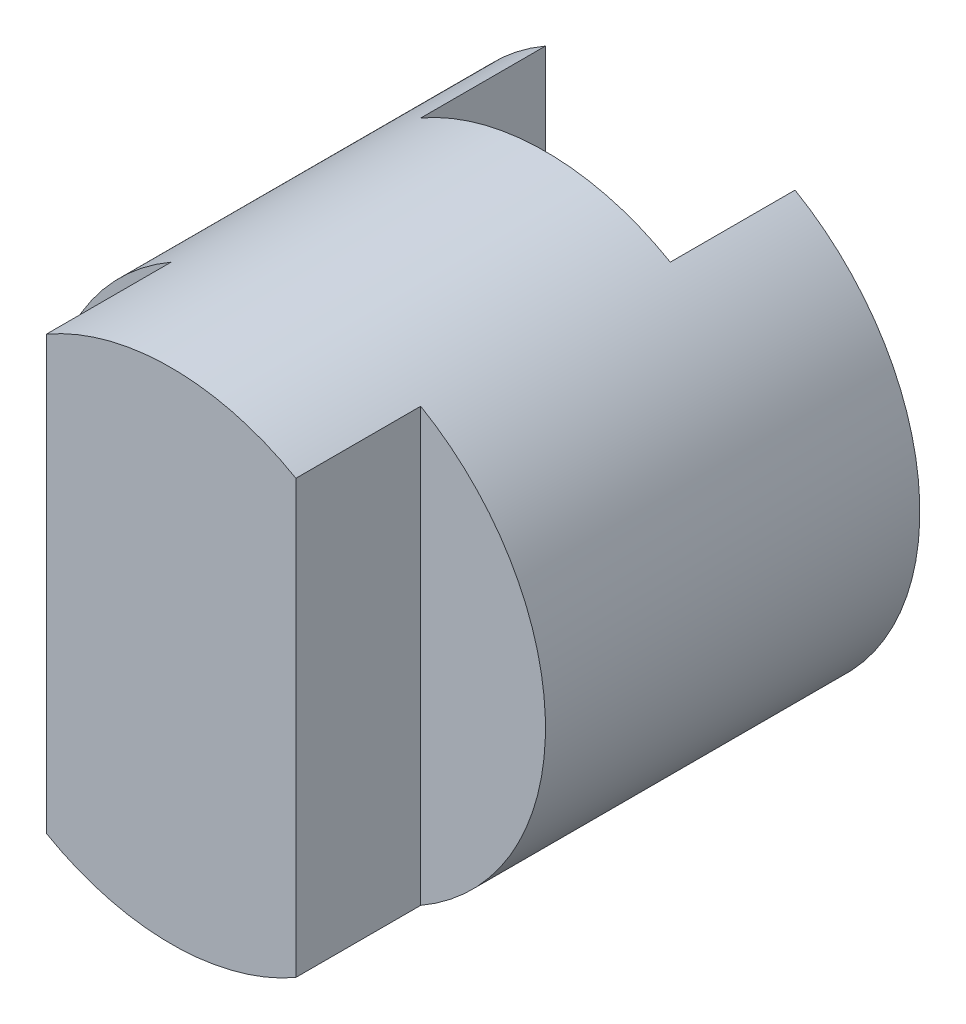
SolidWorks part; units mm, degrees
ref_plane "Front" through (0, 0, 0) normal (0, 0, 1) x (1, 0, 0)
ref_plane "Top" through (0, 0, 0) normal (0, 1, 0) x (1, 0, 0)
ref_plane "Right" through (0, 0, 0) normal (1, 0, 0) x (0, 0, -1)
sketch "Sketch1" plane through (0, 0, 0) normal (0, 0, 1) x (1, 0, 0)
  circle A0 centre (0, 0) radius 2
  dimension "D1" = 4
extrude "Boss-Extrude1" add sketch "Sketch1" along normal blind 4
sketch "Sketch2" plane through (0, 0, 0) normal (0, 1, 0) x (1, 0, 0)
  line L0 (2, -3) -> (1, -3)
  line L1 (2, -4) -> (2, 0) construction
  line L2 (1, -3) -> (1, -4.2215)
  line L3 (1, -4.2215) -> (-1, -4.2646)
  line L4 (-1, -4.2646) -> (-1, -3)
  line L5 (-1, -3) -> (-2.3139, -3)
  line L11 (-2.4898, -4.307) -> (2, -4.619)
  line L12 (2, -4.619) -> (2.5546, -4.2215)
  line L13 (2.5546, -4.2215) -> (2, -3)
  line L14 (-2, -4) -> (2, -4) construction
  line L15 (-2, 0) -> (-2, -4) construction
  line L17 (-2.3139, -3) -> (-2.4898, -4.307)
  line L18 (-1, 0) -> (-1, -0.9997)
  line L19 (2, 0) -> (-2, 0) construction
  line L20 (-1, -0.9997) -> (1, -0.9997)
  line L21 (1, -0.9997) -> (1, 0)
  line L22 (1, 0) -> (-1, 0)
  dimension "D1" = 1
  dimension "D2" = 1
  dimension "D3" = 1.2215
  dimension "D4" = 1
  dimension "D7" = 1
extrude "Cut-Extrude1" cut sketch "Sketch2" against normal mid plane 10
